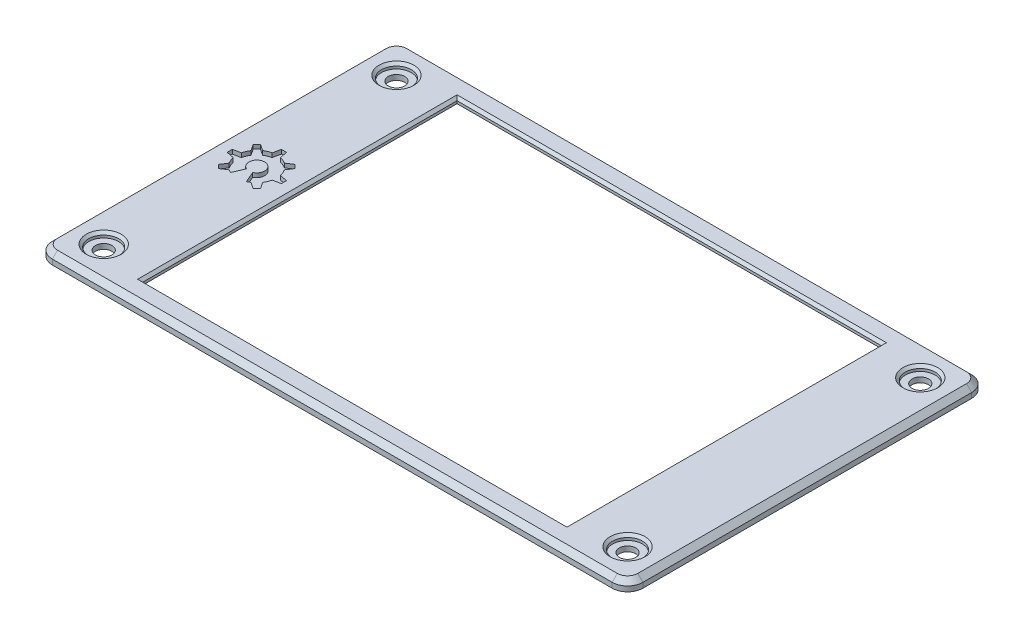
SolidWorks part; units mm, degrees
ref_plane "Front Plane" through (0, 0, 0) normal (0, 0, 1) x (1, 0, 0)
ref_plane "Top Plane" through (0, 0, 0) normal (0, 1, 0) x (1, 0, 0)
ref_plane "Right Plane" through (0, 0, 0) normal (1, 0, 0) x (0, 0, -1)
sketch "Sketch1" plane through (0, 0, 0) normal (0, 1, 0) x (1, 0, 0)
  line L1 (3, 0) -> (112, 0)
  line L2 (0, 3) -> (0, 67)
  line L3 (3, 70) -> (112, 70)
  line L4 (115, 3) -> (115, 67)
  line L5 (16.2, 65.6) -> (98.8, 65.6)
  line L6 (16.2, 65.6) -> (16.2, 4.4)
  line L7 (16.2, 4.4) -> (98.8, 4.4)
  line L8 (98.8, 65.6) -> (98.8, 4.4)
  arc A0 (0, 3) -> (3, 0) centre (3, 3) ccw
  arc A1 (112, 0) -> (115, 3) centre (112, 3) ccw
  arc A2 (115, 67) -> (112, 70) centre (112, 67) ccw
  arc A3 (3, 70) -> (0, 67) centre (3, 67) ccw
  circle A4 centre (6.5, 63.5) radius 1.6
  circle A5 centre (6.5, 6.5) radius 1.6
  circle A6 centre (108.5, 6.5) radius 1.6
  circle A7 centre (108.5, 63.5) radius 1.6
  point P7 (0, 0)
  point P10 (115, 0)
  point P15 (0, 70)
  dimension "D3" = 3
  dimension "D4" = 3.2
  dimension "D1" = 70
  dimension "D2" = 115
  dimension "D5" = 6.5
  dimension "D6" = 6.5
  dimension "D7" = 6.5
  dimension "D8" = 6.5
  dimension "D9" = 82.6
  dimension "D10" = 61.2
  dimension "D11" = 16.2
  dimension "D12" = 4.4
extrude "Boss-Extrude1" add sketch "Sketch1" along normal blind 2
sketch "Sketch2" plane through (0, 0, 0) normal (0, -1, 0) x (1, 0, 0)
  line L8 (15.2, -66.6) -> (99.8, -66.6)
  line L9 (99.8, -66.6) -> (99.8, -3.4)
  line L10 (99.8, -3.4) -> (15.2, -3.4)
  line L11 (15.2, -3.4) -> (15.2, -66.6)
  line L12 (15.2, -66.6) -> (99.8, -66.6)
  line L13 (99.8, -66.6) -> (99.8, -3.4)
  line L14 (99.8, -3.4) -> (15.2, -3.4)
  line L15 (15.2, -3.4) -> (15.2, -66.6)
  dimension "D1" = 1
extrude "Cut-Extrude1" cut sketch "Sketch2" against normal blind 1
chamfer "Chamfer1" distance 0.5 angle 45 4 edges at (98.8, 2, -35) (57.5, 2, -65.6) (16.2, 2, -35) (57.5, 2, -4.4)
sketch "Sketch3" plane through (0, 2, 0) normal (0, 1, 0) x (1, 0, 0)
  circle A0 centre (6.5, 63.5) radius 2.9
  circle A1 centre (108.5, 63.5) radius 2.9
  circle A2 centre (108.5, 6.5) radius 2.9
  circle A3 centre (6.5, 6.5) radius 2.9
  dimension "D1" = 5.8
extrude "Cut-Extrude2" cut sketch "Sketch3" against normal blind 1
chamfer "Chamfer2" distance 0.5 angle 45 4 edges at (108.5, 2, -3.6) (108.5, 2, -60.6) (6.5, 2, -3.6) (6.5, 2, -60.6)
chamfer "Chamfer3" distance 1 angle 45 8 edges at (114.1213, 2, -0.8787) (115, 2, -35) (114.1213, 2, -69.1213) (57.5, 2, -70) (0.8787, 2, -69.1213) (0, 2, -35) (0.8787, 2, -0.8787) (57.5, 2, 0)
sketch "Sketch4" plane through (0, 2, 0) normal (0, 1, 0) x (1, 0, 0)
  line L1 (9.8254, 30.9603) -> (8.8959, 33.1186)
  line L2 (8.2907, 34.5239) -> (12.0383, 38.2715) construction
  line L35 (8.2907, 34.5239) -> (12.0383, 30.7762) construction
  line L36 (8.2907, 39.8002) -> (8.7907, 39.8002)
  line L37 (11.6681, 38.6084) -> (12.0216, 38.2548)
  line L38 (12.0216, 38.2548) -> (12.3752, 37.9013)
  line L39 (13.567, 35.0239) -> (13.567, 34.5239)
  line L40 (13.567, 34.5239) -> (13.567, 34.0239)
  line L41 (12.3752, 31.1465) -> (12.0216, 30.7929)
  line L42 (12.0216, 30.7929) -> (11.6681, 30.4394)
  line L43 (8.7907, 39.8002) -> (9.0907, 38.3205)
  line L44 (10.4096, 37.7742) -> (11.6681, 38.6084)
  line L45 (12.3752, 37.9013) -> (11.541, 36.6428)
  line L46 (13.567, 35.0239) -> (12.0873, 35.3239)
  line L47 (13.567, 34.0239) -> (12.0873, 33.7239)
  line L48 (12.3752, 31.1465) -> (11.541, 32.4049)
  line L49 (11.6681, 30.4394) -> (10.4096, 31.2736)
  line L50 (8.2907, 39.8002) -> (7.7907, 39.8002)
  line L51 (7.7907, 39.8002) -> (7.4907, 38.3205)
  line L52 (6.1717, 37.7742) -> (4.9133, 38.6084)
  line L53 (4.9133, 38.6084) -> (4.5597, 38.2548)
  line L54 (4.5597, 38.2548) -> (4.2062, 37.9013)
  line L55 (4.2062, 37.9013) -> (5.0404, 36.6428)
  line L56 (4.494, 35.3239) -> (3.0143, 35.0239)
  line L57 (3.0143, 35.0239) -> (3.0143, 34.5239)
  line L58 (3.0143, 34.5239) -> (3.0143, 34.0239)
  line L59 (3.0143, 34.0239) -> (4.494, 33.7239)
  line L60 (5.0404, 32.4049) -> (4.2062, 31.1465)
  line L61 (4.2062, 31.1465) -> (4.5597, 30.7929)
  line L62 (4.5597, 30.7929) -> (4.9133, 30.4394)
  line L63 (4.9133, 30.4394) -> (6.1717, 31.2736)
  line L64 (6.756, 30.9603) -> (7.6855, 33.1186)
  circle A0 centre (8.2907, 34.5239) radius 1.53 construction
  circle A1 centre (8.2907, 34.5239) radius 3.88 construction
  circle A2 centre (8.2907, 34.5239) radius 5.3 construction
  arc A3 (6.1717, 31.2736) -> (6.756, 30.9603) centre (8.2907, 34.5239) ccw
  arc A4 (9.8254, 30.9603) -> (10.4096, 31.2736) centre (8.2907, 34.5239) ccw
  arc A5 (11.541, 32.4049) -> (12.0873, 33.7239) centre (8.2907, 34.5239) ccw
  arc A6 (12.0873, 35.3239) -> (11.541, 36.6428) centre (8.2907, 34.5239) ccw
  arc A7 (10.4096, 37.7742) -> (9.0907, 38.3205) centre (8.2907, 34.5239) ccw
  arc A8 (7.4907, 38.3205) -> (6.1717, 37.7742) centre (8.2907, 34.5239) ccw
  arc A9 (5.0404, 36.6428) -> (4.494, 35.3239) centre (8.2907, 34.5239) ccw
  arc A10 (4.494, 33.7239) -> (5.0404, 32.4049) centre (8.2907, 34.5239) ccw
  arc A11 (8.8959, 33.1186) -> (7.6855, 33.1186) centre (8.2907, 34.5239) ccw
extrude "Cut-Extrude3" cut sketch "Sketch4" against normal blind 0.8
